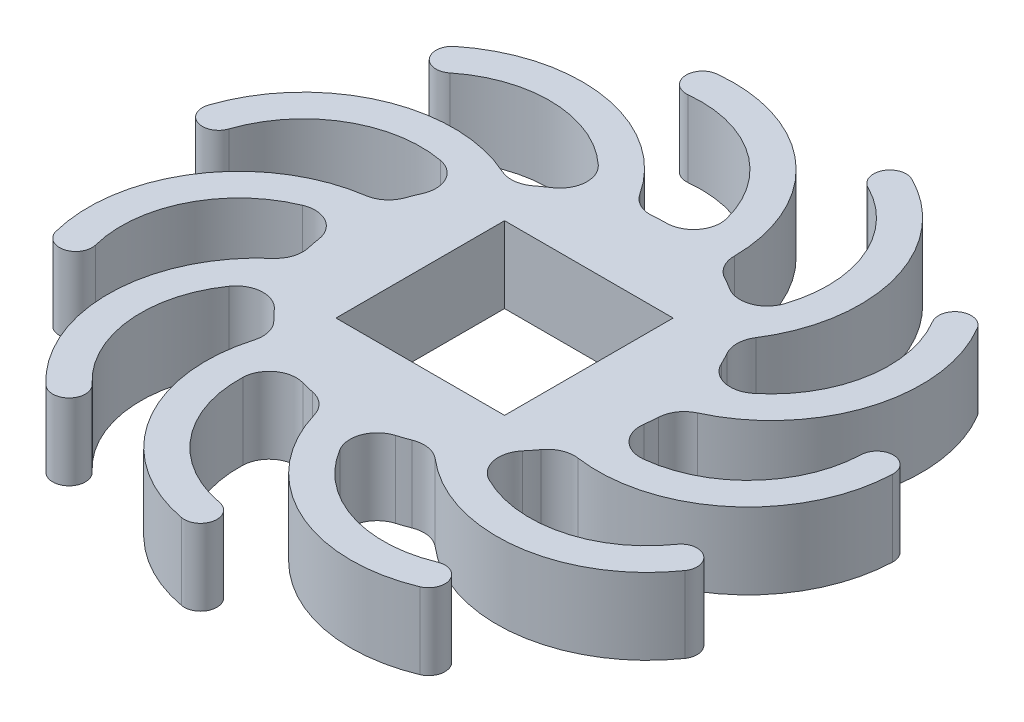
SolidWorks part; units mm, degrees
ref_plane "Front Plane" through (0, 0, 0) normal (0, 0, 1) x (1, 0, 0)
ref_plane "Top Plane" through (0, 0, 0) normal (0, 1, 0) x (1, 0, 0)
ref_plane "Right Plane" through (0, 0, 0) normal (1, 0, 0) x (0, 0, -1)
sketch "Sketch1" plane through (0, 0, 0) normal (0, 1, 0) x (1, 0, 0)
  line L0 (0, 6) -> (5.1962, 9) construction
  line L1 (-3.1, 3.1) -> (3.1, 3.1)
  line L2 (-3.1, 3.1) -> (-3.1, -3.1)
  line L3 (-3.1, -3.1) -> (3.1, -3.1)
  line L4 (3.1, 3.1) -> (3.1, -3.1)
  line L5 (0, -3.1) -> (0, 3.1) construction
  line L6 (-3.1, 0) -> (3.1, 0) construction
  line L7 (5.1962, 9) -> (5.1962, 8.3) construction
  line L8 (5.1962, 8.3) -> (0, 5.3) construction
  line L9 (0, 5.3) -> (0, 6) construction
  line L10 (2.6443, 4.6112) -> (2.9943, 5.2174) construction
  line L11 (2.9943, 5.2174) -> (8.9943, 5.2174) construction
  line L12 (8.9943, 5.2174) -> (8.6443, 4.6112) construction
  line L13 (8.6443, 4.6112) -> (2.6443, 4.6112) construction
  line L14 (4.5899, 2.6924) -> (5.1962, 3.0424) construction
  line L15 (5.1962, 3.0424) -> (10.3923, 0.0424) construction
  line L16 (10.3923, 0.0424) -> (9.7861, -0.3076) construction
  line L17 (9.7861, -0.3076) -> (4.5899, 2.6924) construction
  line L18 (5.3155, 0.058) -> (6.0155, 0.058) construction
  line L19 (6.0155, 0.058) -> (9.0155, -5.1382) construction
  line L20 (9.0155, -5.1382) -> (8.3155, -5.1382) construction
  line L21 (8.3155, -5.1382) -> (5.3155, 0.058) construction
  line L22 (4.6267, -2.5863) -> (5.2329, -2.9363) construction
  line L23 (5.2329, -2.9363) -> (5.2329, -8.9363) construction
  line L24 (5.2329, -8.9363) -> (4.6267, -8.5863) construction
  line L25 (4.6267, -8.5863) -> (4.6267, -2.5863) construction
  line L26 (2.708, -4.532) -> (3.058, -5.1382) construction
  line L27 (3.058, -5.1382) -> (0.058, -10.3343) construction
  line L28 (0.058, -10.3343) -> (-0.292, -9.7281) construction
  line L29 (-0.292, -9.7281) -> (2.708, -4.532) construction
  line L30 (0.0735, -5.2576) -> (0.0735, -5.9576) construction
  line L31 (0.0735, -5.9576) -> (-5.1226, -8.9576) construction
  line L32 (-5.1226, -8.9576) -> (-5.1226, -8.2576) construction
  line L33 (-5.1226, -8.2576) -> (0.0735, -5.2576) construction
  line L34 (-2.5708, -4.5687) -> (-2.9208, -5.1749) construction
  line L35 (-2.9208, -5.1749) -> (-8.9208, -5.1749) construction
  line L36 (-8.9208, -5.1749) -> (-8.5708, -4.5687) construction
  line L37 (-8.5708, -4.5687) -> (-2.5708, -4.5687) construction
  line L38 (-4.5164, -2.65) -> (-5.1226, -3) construction
  line L39 (-5.1226, -3) -> (-10.3188, 0) construction
  line L40 (-10.3188, 0) -> (-9.7126, 0.35) construction
  line L41 (-9.7126, 0.35) -> (-4.5164, -2.65) construction
  line L42 (-5.242, -0.0155) -> (-5.942, -0.0155) construction
  line L43 (-5.942, -0.0155) -> (-8.942, 5.1806) construction
  line L44 (-8.942, 5.1806) -> (-8.242, 5.1806) construction
  line L45 (-8.242, 5.1806) -> (-5.242, -0.0155) construction
  line L46 (-4.5532, 2.6288) -> (-5.1594, 2.9788) construction
  line L47 (-5.1594, 2.9788) -> (-5.1594, 8.9788) construction
  line L48 (-5.1594, 8.9788) -> (-4.5532, 8.6288) construction
  line L49 (-4.5532, 8.6288) -> (-4.5532, 2.6288) construction
  line L50 (-2.6345, 4.5744) -> (-2.9845, 5.1806) construction
  line L51 (-2.9845, 5.1806) -> (0.0155, 10.3768) construction
  line L52 (0.0155, 10.3768) -> (0.3655, 9.7706) construction
  line L53 (0.3655, 9.7706) -> (-2.6345, 4.5744) construction
  circle A0 centre (0, 0) radius 6
  point P62 (0.0368, 0.0212)
  dimension "D1" = 12
  dimension "D2" = 6.2
  dimension "D3" = 6.2
  dimension "D4" = 0.7
  dimension "D5" = 120
  dimension "D6" = 6
  dimension "D7" = 12
extrude "Boss-Extrude1" add sketch "Sketch1" along normal blind 2.8
sketch "Sketch2" plane through (0, 0, 0) normal (0, 1, 0) x (1, 0, 0)
  line L0 (0, -6) -> (6.7694, -9.9083) construction
  line L1 (6.7694, -9.9083) -> (6.7694, -9.2155) construction
  line L2 (6.7694, -9.2155) -> (0, -5.3072) construction
  line L3 (0, -5.3072) -> (0, -6) construction
  line L4 (0, 0) -> (0, -6) construction
  line L5 (-2.4103, -4.5453) -> (-2.7567, -5.1453) construction
  line L6 (-3.1, -3.1) -> (3.1, -3.1) construction
  line L7 (-3.1, -3.1) -> (-3.1, 3.1) construction
  line L8 (-3.1, 3.1) -> (3.1, 3.1) construction
  line L9 (3.1, -3.1) -> (3.1, 3.1) construction
  line L10 (0, 3.1) -> (0, -3.1) construction
  line L11 (-3.1, 0) -> (3.1, 0) construction
  line L12 (-2.7567, -5.1453) -> (1.1516, -11.9147) construction
  line L13 (1.1516, -11.9147) -> (1.498, -11.3147) construction
  line L14 (1.498, -11.3147) -> (-2.4103, -4.5453) construction
  line L15 (-4.1167, -2.6804) -> (-4.7167, -3.0268) construction
  line L16 (-4.7167, -3.0268) -> (-4.7167, -10.8434) construction
  line L17 (-4.7167, -10.8434) -> (-4.1167, -10.497) construction
  line L18 (-4.1167, -10.497) -> (-4.1167, -2.6804) construction
  line L19 (-4.6621, -0.2121) -> (-5.3549, -0.2121) construction
  line L20 (-5.3549, -0.2121) -> (-9.2632, -6.9815) construction
  line L21 (-9.2632, -6.9815) -> (-8.5704, -6.9815) construction
  line L22 (-8.5704, -6.9815) -> (-4.6621, -0.2121) construction
  line L23 (-3.9002, 2.1982) -> (-4.5002, 2.5446) construction
  line L24 (-4.5002, 2.5446) -> (-11.2697, -1.3637) construction
  line L25 (-11.2697, -1.3637) -> (-10.6697, -1.7101) construction
  line L26 (-10.6697, -1.7101) -> (-3.9002, 2.1982) construction
  line L27 (-2.0353, 3.9047) -> (-2.3817, 4.5047) construction
  line L28 (-2.3817, 4.5047) -> (-10.1984, 4.5047) construction
  line L29 (-10.1984, 4.5047) -> (-9.852, 3.9047) construction
  line L30 (-9.852, 3.9047) -> (-2.0353, 3.9047) construction
  line L31 (0.433, 4.45) -> (0.433, 5.1429) construction
  line L32 (0.433, 5.1429) -> (-6.3364, 9.0512) construction
  line L33 (-6.3364, 9.0512) -> (-6.3364, 8.3584) construction
  line L34 (-6.3364, 8.3584) -> (0.433, 4.45) construction
  line L35 (2.8433, 3.6882) -> (3.1897, 4.2882) construction
  line L36 (3.1897, 4.2882) -> (-0.7186, 11.0576) construction
  line L37 (-0.7186, 11.0576) -> (-1.065, 10.4576) construction
  line L38 (-1.065, 10.4576) -> (2.8433, 3.6882) construction
  line L39 (4.5498, 1.8232) -> (5.1498, 2.1696) construction
  line L40 (5.1498, 2.1696) -> (5.1498, 9.9863) construction
  line L41 (5.1498, 9.9863) -> (4.5498, 9.6399) construction
  line L42 (4.5498, 9.6399) -> (4.5498, 1.8232) construction
  line L43 (5.0951, -0.6451) -> (5.7879, -0.6451) construction
  line L44 (5.7879, -0.6451) -> (9.6963, 6.1243) construction
  line L45 (9.6963, 6.1243) -> (9.0034, 6.1243) construction
  line L46 (9.0034, 6.1243) -> (5.0951, -0.6451) construction
  line L47 (4.3333, -3.0554) -> (4.9333, -3.4018) construction
  line L48 (4.9333, -3.4018) -> (11.7027, 0.5065) construction
  line L49 (11.7027, 0.5065) -> (11.1027, 0.853) construction
  line L50 (11.1027, 0.853) -> (4.3333, -3.0554) construction
  line L51 (2.4683, -4.7618) -> (2.8147, -5.3618) construction
  line L52 (2.8147, -5.3618) -> (10.6314, -5.3618) construction
  line L53 (10.6314, -5.3618) -> (10.285, -4.7618) construction
  line L54 (10.285, -4.7618) -> (2.4683, -4.7618) construction
  line L55 (6.7694, -9.5619) -> (0, -5.6536) construction
  line L56 (3.3847, -7.6078) -> (4.8847, -5.0097) construction
  circle A0 centre (0, 0) radius 6 construction
  arc A1 (0, -5.6536) -> (6.7694, -9.5619) centre (4.8847, -5.0097) ccw construction
  arc A2 (-0.5949, -5.732) -> (6.9989, -10.1163) centre (4.8847, -5.0097) ccw
  arc A3 (0.5949, -5.5752) -> (6.5399, -9.0076) centre (4.8847, -5.0097) ccw
  arc A4 (0.5949, -5.5752) -> (-0.5949, -5.732) centre (0, -5.6536) ccw
  arc A5 (6.9989, -10.1163) -> (6.5399, -9.0076) centre (6.7694, -9.5619) ccw
  arc A6 (-2.5137, -5.0117) -> (0.6319, -11.1134) centre (1.4008, -6.8553) ccw
  arc A7 (-2.5137, -5.0117) -> (-3.5994, -4.5005) centre (-3.0566, -4.7561) ccw
  arc A8 (0.4186, -12.2943) -> (0.6319, -11.1134) centre (0.5252, -11.7038) ccw
  arc A9 (-3.5994, -4.5005) -> (0.4186, -12.2943) centre (1.4008, -6.8553) ccw
  arc A10 (-3.0566, -4.7561) -> (0.5252, -11.7038) centre (1.4008, -6.8553) ccw construction
  arc A11 (-4.8242, -2.8571) -> (-5.4768, -9.6908) centre (-2.5278, -6.5244) ccw
  arc A12 (-4.8242, -2.8571) -> (-5.4611, -1.8401) centre (-5.1427, -2.3486) ccw
  arc A13 (-6.2946, -10.5689) -> (-5.4768, -9.6908) centre (-5.8857, -10.1298) ccw
  arc A14 (-5.4611, -1.8401) -> (-6.2946, -10.5689) centre (-2.5278, -6.5244) ccw
  arc A15 (-5.1427, -2.3486) -> (-5.8857, -10.1298) centre (-2.5278, -6.5244) ccw construction
  arc A16 (-5.6031, 0.2046) -> (-9.8466, -5.1914) centre (-5.6539, -4.122) ccw
  arc A17 (-5.6031, 0.2046) -> (-5.589, 1.4045) centre (-5.596, 0.8046) ccw
  arc A18 (-11.0094, -5.488) -> (-9.8466, -5.1914) centre (-10.428, -5.3397) ccw
  arc A19 (-5.589, 1.4045) -> (-11.0094, -5.488) centre (-5.6539, -4.122) ccw
  arc A20 (-5.596, 0.8046) -> (-10.428, -5.3397) centre (-5.6539, -4.122) ccw construction
  arc A21 (-4.603, 3.2014) -> (-11.0902, 0.9562) centre (-6.9849, -0.411) ccw
  arc A22 (-4.603, 3.2014) -> (-3.9424, 4.2032) centre (-4.2727, 3.7023) ccw
  arc A23 (-12.2287, 1.3353) -> (-11.0902, 0.9562) centre (-11.6594, 1.1457) ccw
  arc A24 (-3.9424, 4.2032) -> (-12.2287, 1.3353) centre (-6.9849, -0.411) ccw
  arc A25 (-4.2727, 3.7023) -> (-11.6594, 1.1457) centre (-6.9849, -0.411) ccw construction
  arc A26 (-2.1415, 5.1818) -> (-8.8127, 6.8002) centre (-6.0982, 3.4306) ccw
  arc A27 (-2.1415, 5.1818) -> (-1.0441, 5.6674) centre (-1.5928, 5.4246) ccw
  arc A28 (-9.5655, 7.7347) -> (-8.8127, 6.8002) centre (-9.1891, 7.2674) ccw
  arc A29 (-1.0441, 5.6674) -> (-9.5655, 7.7347) centre (-6.0982, 3.4306) ccw
  arc A30 (-1.5928, 5.4246) -> (-9.1891, 7.2674) centre (-6.0982, 3.4306) ccw construction
  arc A31 (1, 5.5169) -> (-3.7373, 10.4852) centre (-3.2755, 6.1829) ccw
  arc A32 (1, 5.5169) -> (2.1857, 5.3322) centre (1.5928, 5.4246) ccw
  arc A33 (-3.8653, 11.6783) -> (-3.7373, 10.4852) centre (-3.8013, 11.0818) ccw
  arc A34 (2.1857, 5.3322) -> (-3.8653, 11.6783) centre (-3.2755, 6.1829) ccw
  arc A35 (1.5928, 5.4246) -> (-3.8013, 11.0818) centre (-3.2755, 6.1829) ccw construction
  arc A36 (3.8239, 4.1005) -> (2.5247, 10.8412) centre (0.5873, 6.9723) ccw
  arc A37 (3.8239, 4.1005) -> (4.7215, 3.3041) centre (4.2727, 3.7023) ccw
  arc A38 (3.062, 11.9142) -> (2.5247, 10.8412) centre (2.7934, 11.3777) ccw
  arc A39 (4.7215, 3.3041) -> (3.062, 11.9142) centre (0.5873, 6.9723) ccw
  arc A40 (4.2727, 3.7023) -> (2.7934, 11.3777) centre (0.5873, 6.9723) ccw construction
  arc A41 (5.4338, 1.3822) -> (7.9851, 7.7552) centre (4.2635, 5.5479) ccw
  arc A42 (5.4338, 1.3822) -> (5.7583, 0.227) centre (5.596, 0.8046) ccw
  arc A43 (9.0173, 8.3674) -> (7.9851, 7.7552) centre (8.5012, 8.0613) ccw
  arc A44 (5.7583, 0.227) -> (9.0173, 8.3674) centre (4.2635, 5.5479) ccw
  arc A45 (5.596, 0.8046) -> (8.5012, 8.0613) centre (4.2635, 5.5479) ccw construction
  arc A46 (5.3185, -1.7749) -> (10.9103, 2.207) centre (6.5861, 2.3622) ccw
  arc A47 (5.3185, -1.7749) -> (4.9669, -2.9223) centre (5.1427, -2.3486) ccw
  arc A48 (12.1096, 2.164) -> (10.9103, 2.207) centre (11.5099, 2.1855) ccw
  arc A49 (4.9669, -2.9223) -> (12.1096, 2.164) centre (6.5861, 2.3622) ccw
  arc A50 (5.1427, -2.3486) -> (11.5099, 2.1855) centre (6.5861, 2.3622) ccw construction
  arc A51 (3.5146, -4.3685) -> (10.3716, -4.0419) centre (6.8177, -1.5735) ccw
  arc A52 (3.5146, -4.3685) -> (2.5985, -5.1437) centre (3.0566, -4.7561) ccw
  arc A53 (11.3572, -4.7264) -> (10.3716, -4.0419) centre (10.8644, -4.3842) ccw
  arc A54 (2.5985, -5.1437) -> (11.3572, -4.7264) centre (6.8177, -1.5735) ccw
  arc A55 (3.0566, -4.7561) -> (10.8644, -4.3842) centre (6.8177, -1.5735) ccw construction
  point P58 (0.2165, -0.4286)
  point P61 (2.4212, -9.2766)
  point P72 (-2.9784, -9.113)
  point P80 (-7.4324, -6.056)
  point P88 (-9.5267, -1.0764)
  point P96 (-8.5963, 4.245)
  point P104 (-4.9367, 8.2187)
  point P112 (0.2904, 9.5829)
  point P120 (5.4252, 7.9047)
  point P128 (8.8376, 3.7168)
  point P136 (9.4441, -1.6512)
  point P144 (7.0522, -6.4949)
  point P149 (0, 0)
  dimension "D7" = 0.6
  dimension "D1" = 0.6
  dimension "D2" = 12
  dimension "D3" = 6
  dimension "D4" = 120
  dimension "D6" = 3
  dimension "D5" = 12
  dimension "D8" = 11
extrude "Boss-Extrude5" add sketch "Sketch2" along normal blind 2.8
fillet "Fillet1" radius 1 22 edges at (1.0428, 1.4, -5.9087) (-1.1482, 1.4, -5.8891) (-2.3172, 1.4, -5.5345) (-4.1498, 1.4, -4.3335) (-2.6652, 1.4, 5.3755) (-5.6658, 1.4, 1.9746) (-5.8339, 1.4, -1.402) (-4.9415, 1.4, -3.4031) (-5.9969, 1.4, -0.1913) (-5.1484, 1.4, 3.0813) (-3.6988, 1.4, 4.7243) (-0.5575, 1.4, 5.974) (2.7608, 1.4, 5.3271) (0.6641, 1.4, 5.9631) (5.2026, 1.4, 2.9888) (3.7826, 1.4, 4.6575) (5.7001, 1.4, 1.8731) (5.9926, 1.4, -0.2984) (4.88, 1.4, -3.4909) (5.8079, 1.4, -1.506) (2.218, 1.4, -5.575) (4.0717, 1.4, -4.4069)
